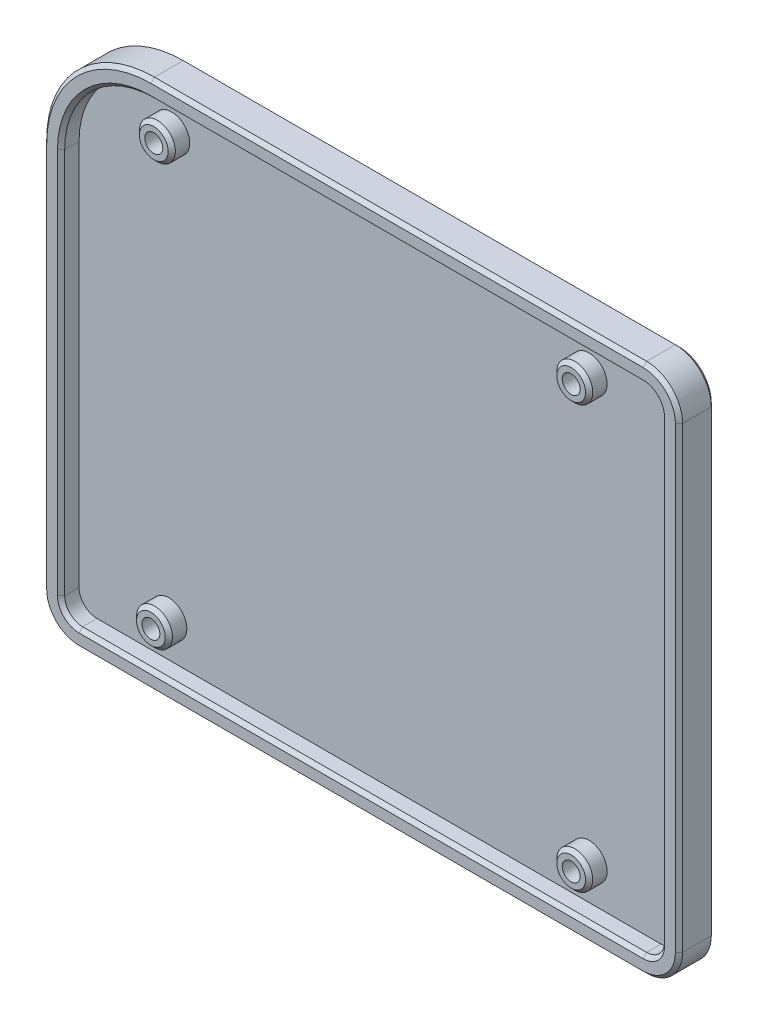
SolidWorks part; units mm, degrees
material "ABS"
ref_plane "Front Plane" through (0, 0, 0) normal (0, 0, 1) x (1, 0, 0)
ref_plane "Top Plane" through (0, 0, 0) normal (0, 1, 0) x (1, 0, 0)
ref_plane "Right Plane" through (0, 0, 0) normal (1, 0, 0) x (0, 0, -1)
sketch "Sketch1" plane through (0, 0, 0) normal (0, 0, 1) x (1, 0, 0)
  line L1 (-88.5, -73.75) -> (88.5, -73.75)
  line L2 (-88.5, -73.75) -> (-88.5, 73.75)
  line L3 (-88.5, 73.75) -> (88.5, 73.75)
  line L4 (88.5, -73.75) -> (88.5, 73.75)
  line L5 (-88.5, -73.75) -> (88.5, 73.75) construction
  line L6 (-88.5, 73.75) -> (88.5, -73.75) construction
  point P0 (0, 0)
  dimension "D1" = 177
  dimension "D2" = 147.5
extrude "Boss-Extrude1" add sketch "Sketch1" along normal mid plane 20
fillet "Fillet2" radius 30 1 edges at (-88.5, 73.75, 0)
fillet "Fillet3" radius 10 3 edges at (-88.5, -73.75, 0) (88.5, -73.75, 0) (88.5, 73.75, 0)
sketch "Sketch6" plane through (0, 0, 0) normal (0, 1, 0) x (1, 0, 0)
  line L0 (-88.5, -10) -> (-88.5, 0)
  line L1 (-88.5, -10) -> (-88.5, 10) construction
  line L2 (-88.5, 0) -> (88.5, 0)
  line L3 (88.5, 10) -> (88.5, -10) construction
  line L4 (88.5, 0) -> (88.5, -10)
  line L5 (88.5, -10) -> (-88.5, -10)
extrude "Cut-Extrude14" cut sketch "Sketch6" against normal through all both and the other way through all
shell "Shell1" thickness 5
chamfer "Chamfer1" distance 1 angle 45 24 edges at (85.5711, -70.8211, -10) (0, -73.75, -10) (88.5, 0, -10) (-85.5711, -70.8211, -10) (85.5711, 70.8211, -10) (-88.5, -10, -10) (10, 73.75, -10) (-79.7132, 64.9632, -10) (85.5711, -70.8211, 0) (88.5, 0, 0) (0, -73.75, 0) (85.5711, 70.8211, 0) (-85.5711, -70.8211, 0) (10, 73.75, 0) (-88.5, -10, 0) (-79.7132, 64.9632, 0) (82.0355, -67.2855, 0) (83.5, 0, 0) (0, -68.75, 0) (82.0355, 67.2855, 0) (-82.0355, -67.2855, 0) (10, 68.75, 0) (-83.5, -10, 0) (-76.1777, 61.4277, 0)
hole_wizard "Tap Drill for M6x1.0 Tap1" positions "Sketch7" profile "Sketch8" hole size "M6x1.0" standard "ANSI Metric"
sketch "Sketch7" plane through (-88.5, -73.75, -10) normal (0, 0, -1) x (-1, 0, 0)
  point P0 (-147, 132.5)
  point P3 (-30.8074, 132.5)
  point P6 (-30, 15)
  point P9 (-147, 14.9999)
sketch "Sketch8" plane through (58.5, 58.75, -10) normal (1, 0, 0) x (0, 1, 0)
  line L0 (0, 0) -> (0, 19.5022)
  line L1 (0, 19.5022) -> (2.5, 18)
  line L2 (2.5, 18) -> (2.5, 0)
  line L3 (2.5, 0) -> (0, 0)
  line L4 (0, 19.5022) -> (-2.5, 18) construction
  line L5 (0, -6.35) -> (0, 107.95) construction
  dimension "Hole Dia." = 5
  dimension "Hole Depth" = 18
  dimension "Drill Angle" = 118
sketch "Sketch9" plane through (0, 0, -5) normal (0, 0, 1) x (1, 0, 0)
  circle A0 centre (-57.6926, 58.75) radius 2.5
  circle A1 centre (-57.6926, 58.75) radius 5
  circle A2 centre (58.5, 58.75) radius 2.5
  circle A3 centre (58.5, 58.75) radius 5
  circle A4 centre (58.5, -58.7501) radius 2.5
  circle A5 centre (58.5, -58.7501) radius 5
  circle A6 centre (-58.5, -58.75) radius 2.5
  circle A7 centre (-58.5, -58.75) radius 5
  dimension "D1" = 5
  dimension "D2" = 10
  dimension "D3" = 10
  dimension "D4" = 5
  dimension "D5" = 5
  dimension "D6" = 10
  dimension "D7" = 10
  dimension "D8" = 5
extrude "Boss-Extrude2" add sketch "Sketch9" along normal up to surface (5 mm away) up to face at (1.9822, -1.9822, 0)
chamfer "Chamfer2" distance 1 angle 45 4 edges at (53.5, -58.7501, 0) (53.5, 58.75, 0) (-62.6926, 58.75, 0) (-63.5, -58.75, 0)
